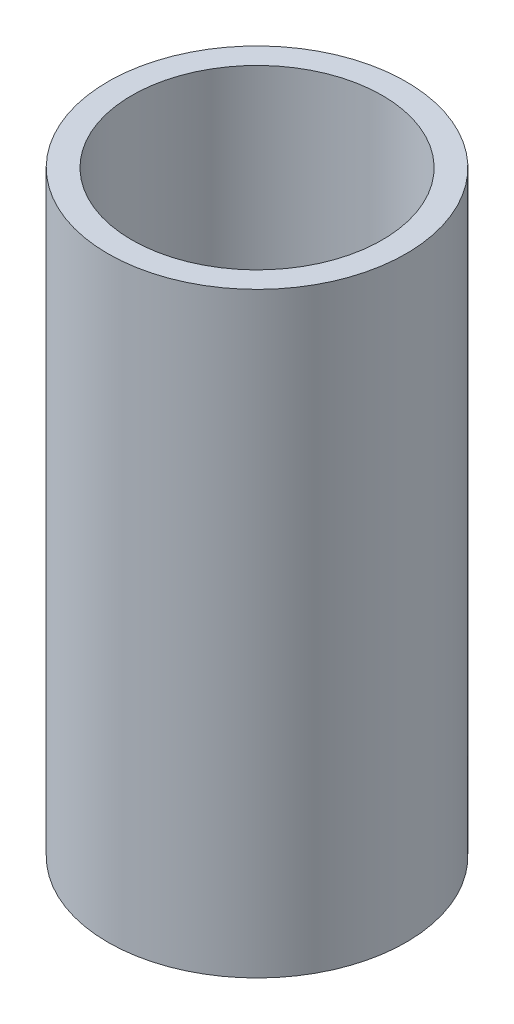
SolidWorks part; units mm, degrees
ref_plane "Front Plane" through (0, 0, 0) normal (0, 0, 1) x (1, 0, 0)
ref_plane "Top Plane" through (0, 0, 0) normal (0, 1, 0) x (1, 0, 0)
ref_plane "Right Plane" through (0, 0, 0) normal (1, 0, 0) x (0, 0, -1)
sketch "Sketch1" plane through (0, 0, 0) normal (0, 1, 0) x (1, 0, 0)
  circle A0 centre (0, 0) radius 2.1
  circle A1 centre (0, 0) radius 2.5
  dimension "D1" = 4.2
  dimension "D2" = 5
extrude "Boss-Extrude1" add sketch "Sketch1" along normal blind 10
